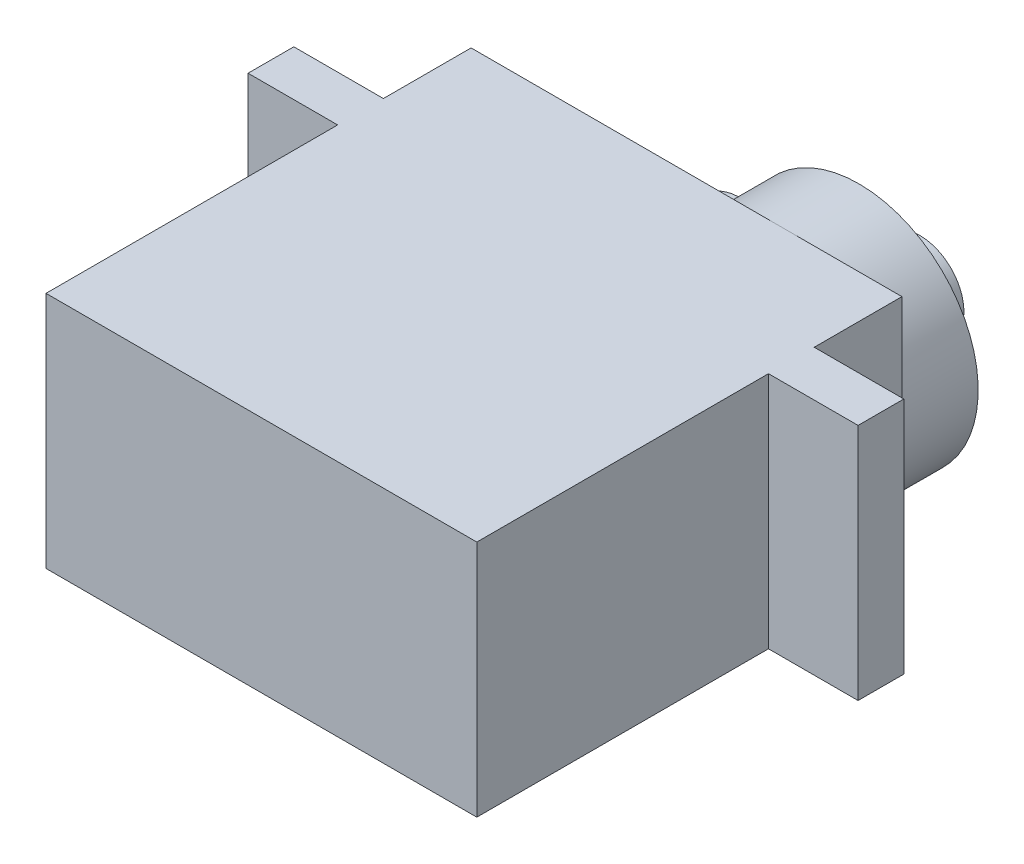
SolidWorks part; units mm, degrees
ref_plane "Front Plane" through (0, 0, 0) normal (0, 0, 1) x (1, 0, 0)
ref_plane "Top Plane" through (0, 0, 0) normal (0, 1, 0) x (1, 0, 0)
ref_plane "Right Plane" through (0, 0, 0) normal (1, 0, 0) x (0, 0, -1)
sketch "Sketch1" plane through (0, 0, 0) normal (0, 1, 0) x (1, 0, 0)
  line L0 (0, 17.7) -> (0, 22.3)
  line L1 (0, 0) -> (22.6, 0)
  line L2 (0, 0) -> (0, 15.3)
  line L3 (0, 22.3) -> (22.6, 22.3)
  line L4 (22.6, 0) -> (22.6, 15.3)
  line L5 (-4.7, 17.7) -> (0, 17.7)
  line L6 (-4.7, 17.7) -> (-4.7, 15.3)
  line L7 (-4.7, 15.3) -> (0, 15.3)
  line L9 (22.6, 17.7) -> (22.6, 22.3)
  line L10 (22.6, 17.7) -> (27.3, 17.7)
  line L12 (22.6, 15.3) -> (27.3, 15.3)
  line L13 (27.3, 17.7) -> (27.3, 15.3)
  point P13 (0, 0)
  point P14 (0, 0)
  dimension "D1" = 22.3
  dimension "D2" = 22.6
  dimension "D3" = 32
  dimension "D4" = 2.4
  dimension "D5" = 4.6
extrude "Boss-Extrude1" add sketch "Sketch1" along normal blind 12.5
sketch "Sketch2" plane through (0, 0, -22.3) normal (0, 0, -1) x (-1, 0, 0)
  line L0 (-22.6, 12.5) -> (-22.6, 0) construction
  line L2 (-22.6, 12.5) -> (0, 12.5) construction
  line L3 (-22.6, 0) -> (0, 0) construction
  arc A0 (-10.6, 8.6995) -> (-10.6, 3.8005) centre (-16.35, 6.25) ccw
  arc A1 (-10.6, 3.8005) -> (-10.6, 8.6995) centre (-10.1, 6.25) ccw
  dimension "D1" = 5
extrude "Boss-Extrude2" add sketch "Sketch2" along normal blind 4
sketch "Sketch3" plane through (0, 0, -26.3) normal (0, 0, -1) x (-1, 0, 0)
  circle A0 centre (-16.35, 6.25) radius 2.3
  arc A2 (-10.6, 8.6995) -> (-10.6, 3.8005) centre (-16.35, 6.25) ccw construction
  dimension "D1" = 4.6
extrude "Boss-Extrude3" add sketch "Sketch3" along normal blind 3.2
